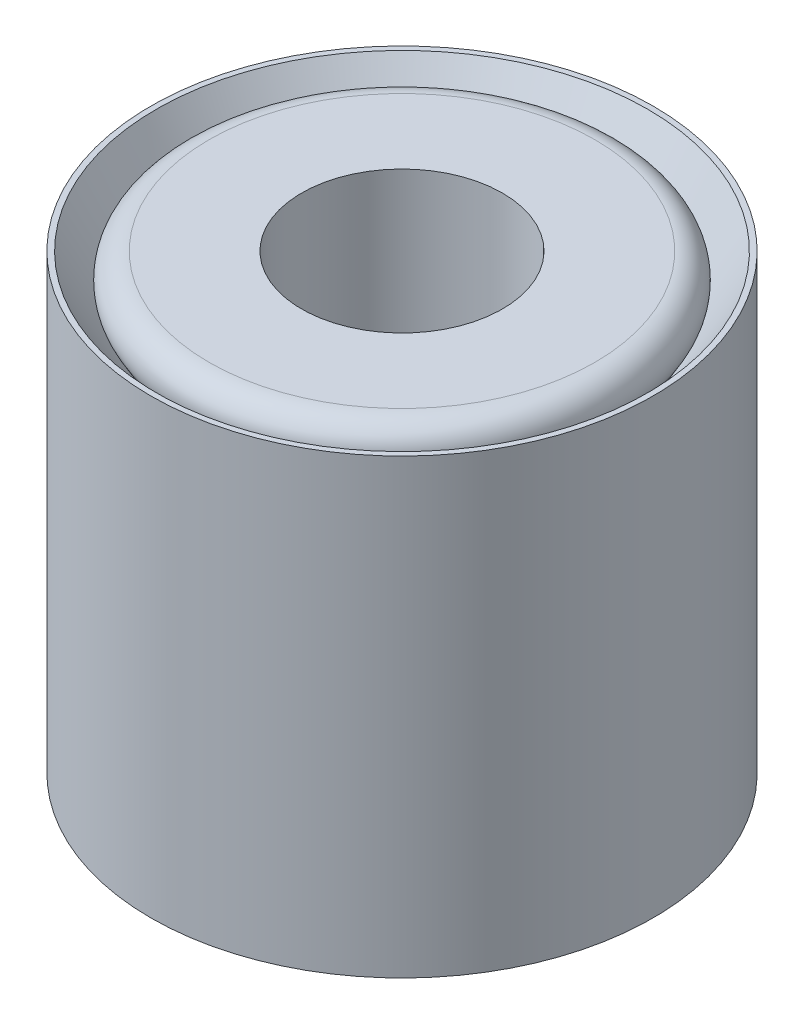
SolidWorks part; units mm, degrees
ref_plane "Front Plane" through (0, 0, 0) normal (0, 0, 1) x (1, 0, 0)
ref_plane "Top Plane" through (0, 0, 0) normal (0, 1, 0) x (1, 0, 0)
ref_plane "Right Plane" through (0, 0, 0) normal (1, 0, 0) x (0, 0, -1)
sketch "Sketch1" plane through (0, 0, 0) normal (0, 0, 1) x (1, 0, 0)
  line L0 (-3.5, 0) -> (3.5, 0) construction
  line L1 (0, -4.5) -> (0, 4.5) construction
  line L2 (5, -4.5) -> (4.8914, -4.5)
  line L3 (5, -4.5) -> (5, 4.5)
  line L4 (5, 4.5) -> (4.8914, 4.5)
  line L5 (2, -4.5) -> (2, 4.5)
  line L6 (5, -4.5) -> (2, 4.5) construction
  line L7 (5, 4.5) -> (2, -4.5) construction
  line L8 (3.5, 4.5) -> (3.5, 0) construction
  line L9 (3.5, 0) -> (3.5, -4.5) construction
  line L10 (2.201, 0) -> (4.799, 4.5) construction
  line L11 (2.201, 0) -> (4.799, -4.5) construction
  line L12 (4.799, -4.5) -> (4.799, 4.5) construction
  line L13 (2.2933, 0) -> (4.8914, -4.5)
  line L14 (2.2933, 0) -> (4.8914, 4.5)
  line L15 (2.1086, 0) -> (4.7067, -4.5)
  line L16 (2.1086, 0) -> (4.7067, 4.5)
  line L17 (2.2933, 0) -> (4.8683, 4.46) construction
  line L18 (2.1086, 0) -> (4.7298, 4.54) construction
  line L19 (2.2933, 0) -> (4.8683, -4.46) construction
  line L20 (2.1086, 0) -> (4.7298, -4.54) construction
  line L21 (4.7067, -4.5) -> (2, -4.5)
  line L22 (4.7067, 4.5) -> (2, 4.5)
  point P4 (0, 0)
  point P12 (0, 0)
  point P14 (-5, 4.5)
  point P15 (-2, 4.5)
  point P19 (3.5, 2.25)
  dimension "D1" = 4
  dimension "10" = 10
  dimension "D3" = 9
  dimension "D4" = 120
  dimension "D5" = 0.08
  dimension "D6" = 0.08
revolve "Revolve1" add sketch "Sketch1" angle 360 about L1
fillet "Fillet1" radius 1 1 edges at (0, 0, -2.2933)
fillet "Fillet8" radius 0.5 3 edges at (0, -4.5, -2) (0, -4.5, -4.7067) (0, 4.5, -4.7067)
